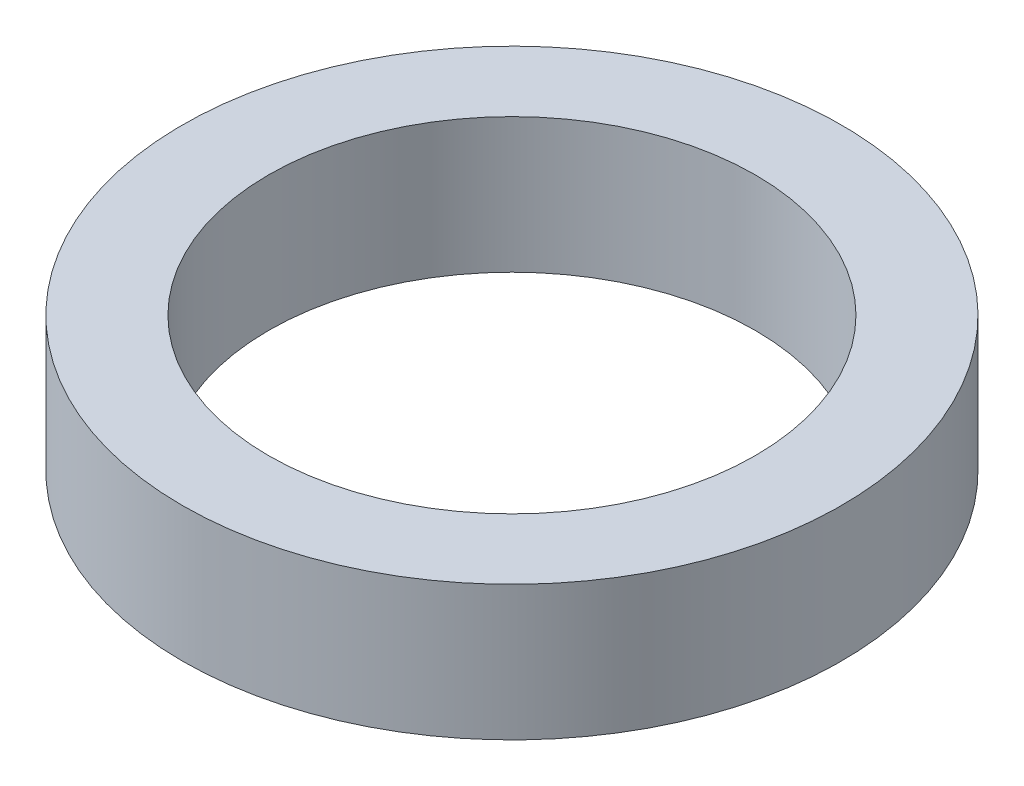
SolidWorks part; units mm, degrees
ref_plane "Front Plane" through (0, 0, 0) normal (0, 0, 1) x (1, 0, 0)
ref_plane "Top Plane" through (0, 0, 0) normal (0, 1, 0) x (1, 0, 0)
ref_plane "Right Plane" through (0, 0, 0) normal (1, 0, 0) x (0, 0, -1)
sketch "Sketch1" plane through (0, 0, 0) normal (0, 1, 0) x (1, 0, 0)
  circle A0 centre (0, 0) radius 13.97
  circle A1 centre (0, 0) radius 10.3124
  dimension "D1" = 20.6248
  dimension "D2" = 27.94
extrude "Boss-Extrude1" add sketch "Sketch1" along normal blind 5.7125
